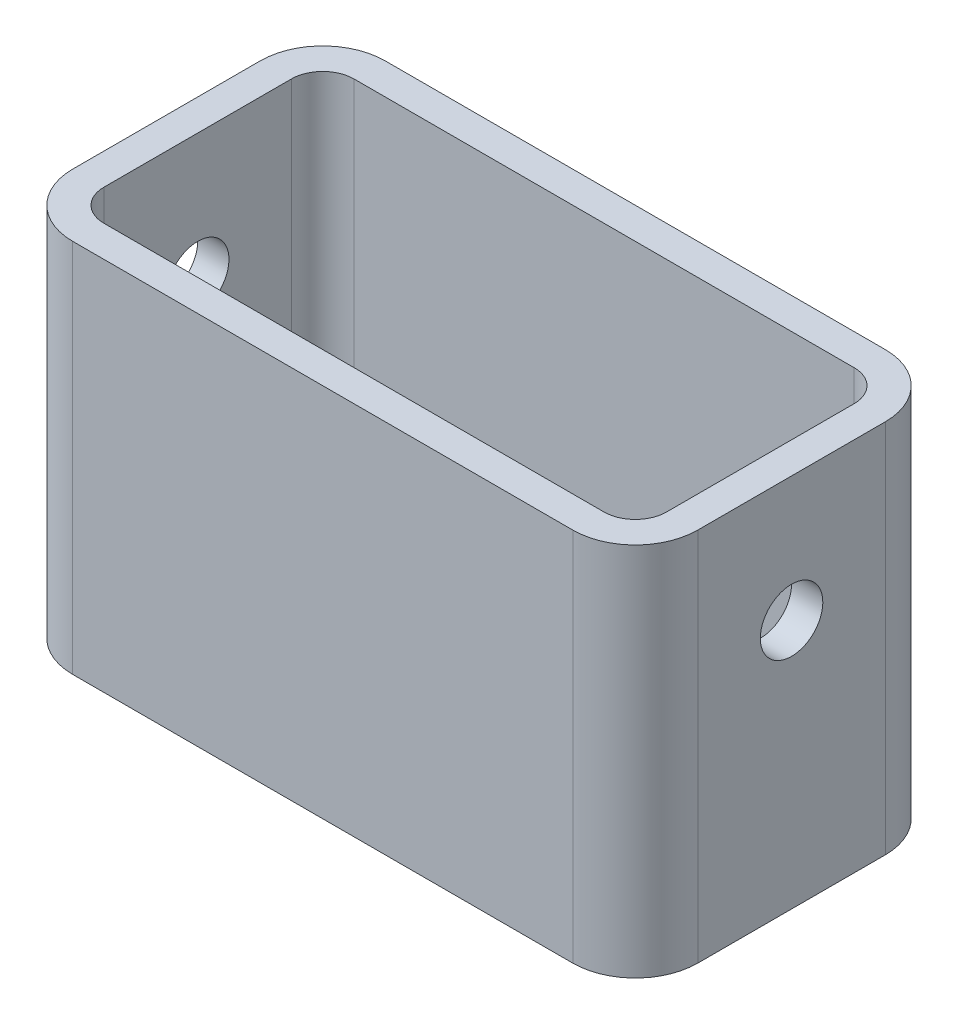
SolidWorks part; units mm, degrees
ref_plane "Front Plane" through (0, 0, 0) normal (0, 0, 1) x (1, 0, 0)
ref_plane "Top Plane" through (0, 0, 0) normal (0, 1, 0) x (1, 0, 0)
ref_plane "Right Plane" through (0, 0, 0) normal (1, 0, 0) x (0, 0, -1)
sketch "Sketch1" plane through (0, 0, 0) normal (0, 0, 1) x (1, 0, 0)
  line L1 (0, 0) -> (100, 0)
  line L2 (0, 0) -> (0, 60)
  line L3 (0, 60) -> (100, 60)
  line L4 (100, 0) -> (100, 60)
  dimension "D1" = 100
  dimension "D2" = 60
extrude "Boss-Extrude1" add sketch "Sketch1" along normal blind 50
fillet "Fillet1" radius 10 4 edges at (0, 30, 0) (100, 30, 0) (0, 30, 50) (100, 30, 50)
shell "Shell1" thickness 5
sketch "Sketch2" plane through (100, 0, 0) normal (1, 0, 0) x (0, 0, -1)
  line L0 (-50, 0) -> (-50, 60) construction
  line L1 (-40, 0) -> (-10, 0) construction
  circle A0 centre (-25, 40) radius 5
  dimension "D3" = 10
  dimension "D1" = 25
  dimension "D2" = 40
extrude "Cut-Extrude1" cut sketch "Sketch2" against normal through all
